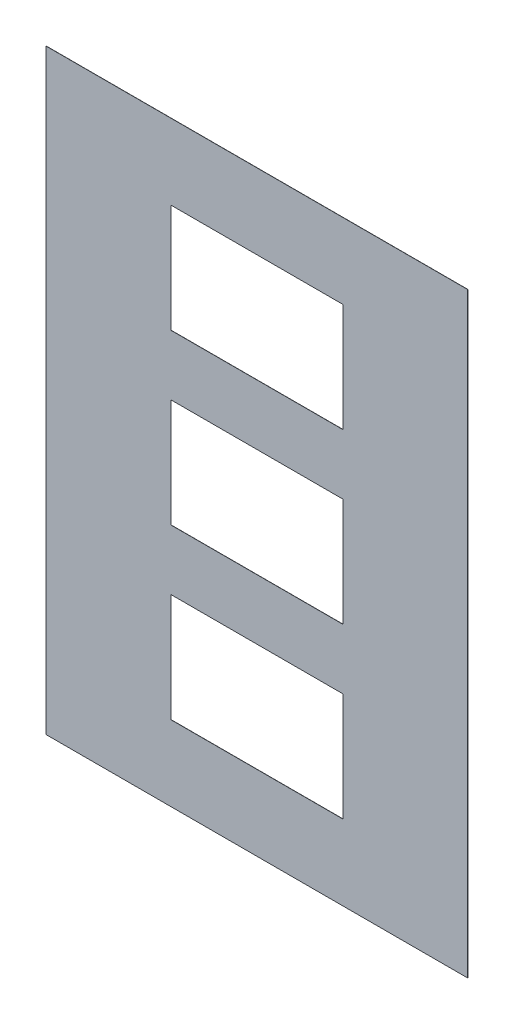
SolidWorks part; units mm, degrees
ref_plane "前视基准面" through (0, 0, 0) normal (0, 0, 1) x (1, 0, 0)
ref_plane "上视基准面" through (0, 0, 0) normal (0, 1, 0) x (1, 0, 0)
ref_plane "右视基准面" through (0, 0, 0) normal (1, 0, 0) x (0, 0, -1)
sketch "草图1" plane through (0, 0, 0) normal (0, 0, 1) x (1, 0, 0)
  line L1 (0, 0) -> (210, 0)
  line L2 (0, 0) -> (0, 297)
  line L3 (0, 297) -> (210, 297)
  line L4 (210, 0) -> (210, 297)
  dimension "D1" = 297
  dimension "D2" = 210
extrude "凸台-拉伸1" add sketch "草图1" along normal blind 0.1
sketch "草图2" plane through (0, 0, 0.1) normal (0, 0, 1) x (1, 0, 0)
  line L0 (105, 0) -> (105, 297) construction
  line L1 (0, 0) -> (210, 0) construction
  line L2 (210, 297) -> (0, 297) construction
  line L4 (147.8, 91.5) -> (62.2, 91.5)
  line L5 (147.8, 91.5) -> (147.8, 37.5)
  line L6 (147.8, 37.5) -> (62.2, 37.5)
  line L7 (62.2, 91.5) -> (62.2, 37.5)
  dimension "D1" = 85.6
  dimension "D2" = 54
  dimension "D3" = 37.5
extrude "切除-拉伸1" cut sketch "草图2" against normal blind 8
pattern_linear "阵列(线性)1" count 3 spacing 84 along (0, 1, 0) of "切除-拉伸1"
